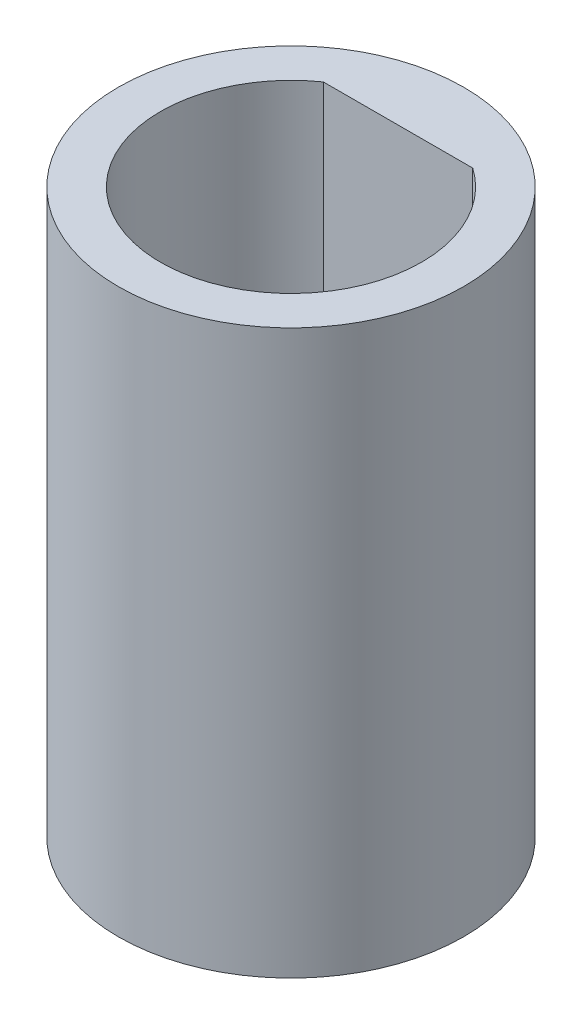
SolidWorks part; units mm, degrees
material "1060 Alloy"
ref_plane "Front Plane" through (0, 0, 0) normal (0, 0, 1) x (1, 0, 0)
ref_plane "Top Plane" through (0, 0, 0) normal (0, 1, 0) x (1, 0, 0)
ref_plane "Right Plane" through (0, 0, 0) normal (1, 0, 0) x (0, 0, -1)
sketch "Sketch1" plane through (0, 0, 0) normal (0, 1, 0) x (1, 0, 0)
  circle A0 centre (0, 0) radius 5.842
extrude "Boss-Extrude1" add sketch "Sketch1" along normal blind 19.05
sketch "Sketch4" plane through (0, 19.05, 0) normal (0, 1, 0) x (1, 0, 0)
  line L0 (-2.5277, 3.622) -> (2.5224, 3.6257)
  arc A0 (-2.5277, 3.622) -> (2.5224, 3.6257) centre (0, 0) ccw
extrude "Cut-Extrude3" cut sketch "Sketch4" against normal blind 19.0501
sketch3d "3DSketch1"
